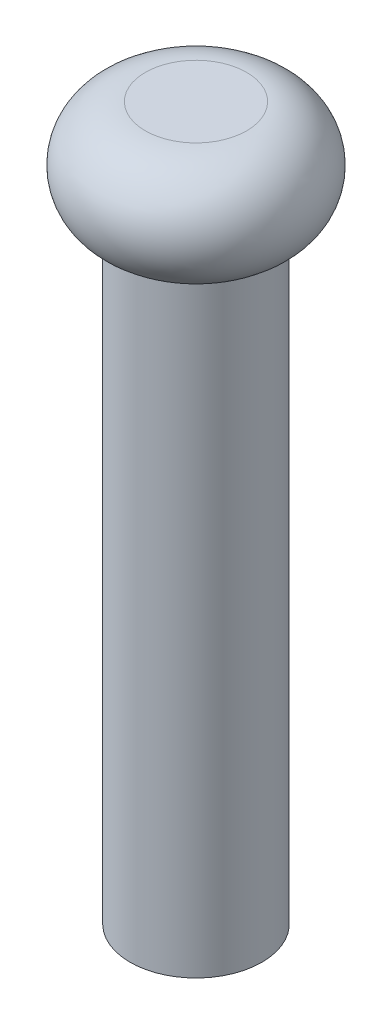
SolidWorks part; units mm, degrees
ref_plane "Front Plane" through (0, 0, 0) normal (0, 0, 1) x (1, 0, 0)
ref_plane "Top Plane" through (0, 0, 0) normal (0, 1, 0) x (1, 0, 0)
ref_plane "Right Plane" through (0, 0, 0) normal (1, 0, 0) x (0, 0, -1)
sketch "Sketch1" plane through (0, 0, 0) normal (0, 0, 1) x (1, 0, 0)
  line L0 (0, -100.3257) -> (0, 4915.9595) construction
  line L1 (0, 0) -> (1.25, 0)
  line L2 (1.25, 0) -> (1.25, 11.5)
  line L3 (1.25, 11.5) -> (1.36, 11.5)
  line L4 (0.96, 13.5) -> (0, 13.5)
  line L6 (0, 0) -> (0, 13.5)
  arc A0 (1.36, 11.5) -> (0.96, 13.5) centre (0.96, 12.46) ccw
  point P9 (0.9664, 13.5)
  point P11 (1, 11.5)
  point P12 (1.3498, 11.5)
  point P13 (0.9834, 13.5)
  dimension "D5" = 1.04
  dimension "D1" = 4
  dimension "D2" = 2
  dimension "D3" = 13.5
  dimension "D4" = 2.5
revolve "Revolve1" add sketch "Sketch1" angle 360 about L0
